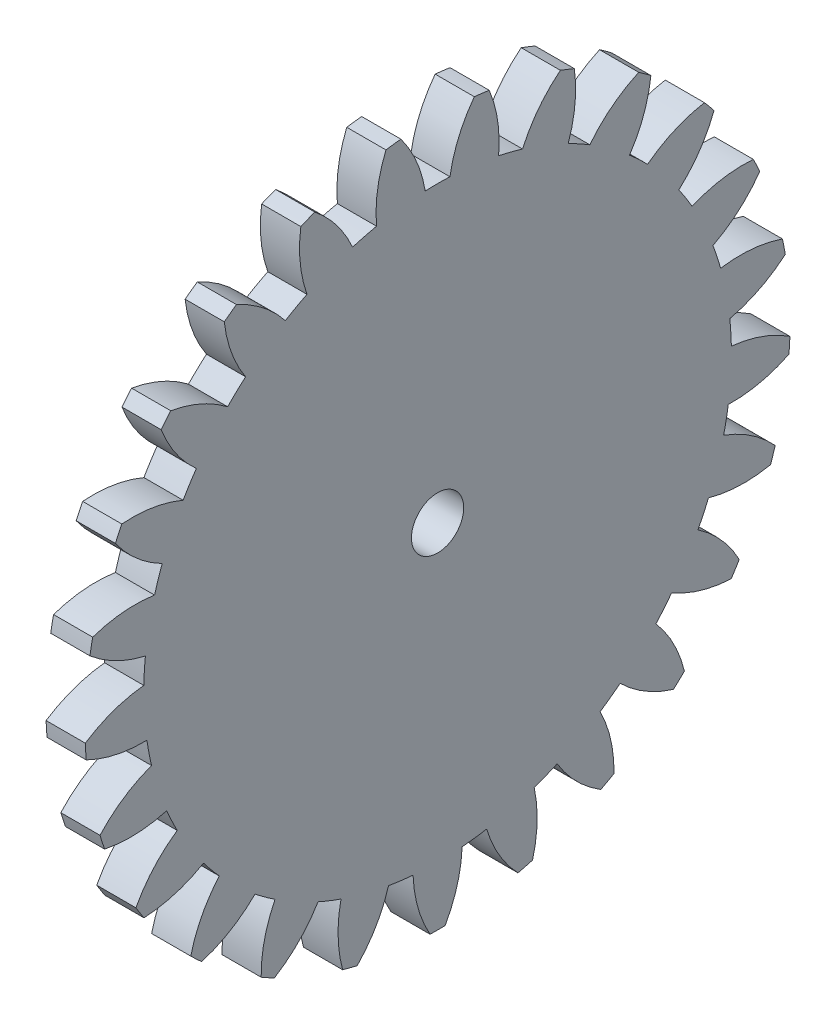
SolidWorks part; units mm, degrees
ref_plane "Plane1" through (0, 0, 0) normal (0, 0, 1) x (1, 0, 0)
ref_plane "Plane2" through (0, 0, 0) normal (0, 1, 0) x (1, 0, 0)
ref_plane "Plane3" through (0, 0, 0) normal (1, 0, 0) x (0, 0, -1)
other "Configuration Table"
sketch "HoldingSke" plane through (0, 0, 0) normal (0, 1, 0) x (1, 0, 0)
  line L0 (0, 0) -> (0.4532, -0.2113)
  line L1 (-15, 0) -> (100, 0) construction
  line L2 (0, 0) -> (-2.1039, 2.3779)
  line L3 (0, 0) -> (-11.863, 4.5341)
  line L4 (0, 0) -> (7.8269, 3.6497)
  line L5 (0, 0) -> (-46.8476, -17.4728)
  line L6 (0, 0) -> (-2.4869, -1.6779)
  line L7 (-2.1039, 2.3779) -> (8.6586, 51.2059)
  line L8 (-76.2, 54.61) -> (-75.5, 54.61)
  line L9 (-71.009, 38.7566) -> (-53.1078, 45.2721)
  line L10 (-76.2, 71.12) -> (104.1128, 71.12)
  line L11 (0, 0) -> (-3, 0)
  line L12 (-76.2, 101.6) -> (-76.133, 101.6)
  line L13 (24.9733, 27.94) -> (52.9518, 28.4284)
  line L14 (24.9733, 27.94) -> (24.9743, 27.94)
  line L15 (24.9733, 27.94) -> (100.4006, 29.5858)
  line L16 (-63.627, -2) -> (-12.827, -2)
  circle A0 centre (0, 0) radius 2
  circle A1 centre (0, 0) radius 22.499
  circle A2 centre (0, 0) radius 37.5
  circle A3 centre (0, 0) radius 2
  dimension "Hub_dia" = 75
  dimension "Bore" = 4
  dimension "MBD" = 4
  dimension "Num_teeth" = 25
  dimension "Overall_len" = 50
  dimension "Show_teeth" = 25
  dimension "Thickness" = 3
  dimension "OAL" = 50.0001
  dimension "T_dim" = 0.7
  dimension "Ap" = 20
  dimension "H" = 19.05
  dimension "Pitch_radius" = 180.3128
  dimension "Width" = 3
  dimension "Addendum_fac" = 1
  dimension "Dedendum_fac" = 1.25
  dimension "Clearance_fac" = 0.25
  dimension "Dedendum_add" = 0.001
sketch "BasProSke" plane through (0, 0, 0) normal (0, 1, 0) x (1, 0, 0)
  line L0 (-10, 0) -> (60, 0) construction
  line L1 (0, 0) -> (0, 27)
  line L2 (0, 0) -> (3, 0)
  line L3 (3, 0) -> (3, 27)
  line L4 (3, 27) -> (0, 27)
  dimension "Thickness" = 3
revolve "Base-Revolve" add sketch "BasProSke" angle 360 about L0
sketch "TooCutSke" plane through (0, 0, 0) normal (1, 0, 0) x (0, 0, -1)
  line L1 (0, 0) -> (0, 107) construction
  line L2 (0, 0) -> (-1.687, 24.943) construction
  line L3 (0, 0) -> (-6.2561, 49.5219) construction
  line L4 (-1.687, 24.943) -> (-3.128, 24.761) construction
  arc A0 (0.9462, 22.4791) -> (-0.9462, 22.4791) centre (0, 0) ccw
  arc A1 (2.8295, 26.8769) -> (-2.8295, 26.8769) centre (0, 0) ccw
  circle A2 centre (0, 0) radius 25 construction
  circle A3 centre (0, 0) radius 23.4923 construction
  arc A4 (-0.9462, 22.4791) -> (-2.8295, 26.8769) centre (-10.8135, 20.8556) ccw
  arc A5 (2.8295, 26.8769) -> (0.9462, 22.4791) centre (10.8135, 20.8556) ccw
  dimension "Half_ang" = 7.2
extrude "ToothCut" cut sketch "TooCutSke" along normal through all
fillet "Breaks" [suppressed] radius 0.04
fillet "RootFillets" [suppressed] radius 0.501
pattern_circular "TeethCuts" count 25 every 14.4 about axis through (-10, 0, 0) along (1, 0, 0) of "ToothCut", "RootFillets", "Breaks"
sketch "HubNeaOneSke" plane through (0, 0, 0) normal (-1, 0, 0) x (0, 0, 1)
  circle A0 centre (0, 0) radius 22.499
extrude "HubNearOne" [suppressed] add sketch "HubNeaOneSke" along normal blind 47.0001
sketch "HubNeaBotSke" plane through (0, 0, 0) normal (-1, 0, 0) x (0, 0, 1)
  circle A0 centre (0, 0) radius 22.499
extrude "HubNearBoth" [suppressed] add sketch "HubNeaBotSke" along normal blind 23.5
ref_plane "FarPln" through (3, 0, 0) normal (1, 0, 0) x (0, 0, -1)
sketch "HubFarSke" plane through (3, 0, 0) normal (1, 0, 0) x (0, 0, -1)
  circle A0 centre (0, 0) radius 22.499
extrude "HubFar" [suppressed] add sketch "HubFarSke" along normal blind 23.5
sketch "BorSke" plane through (0, 0, 0) normal (1, 0, 0) x (0, 0, -1)
  circle A0 centre (0, 0) radius 2
  dimension "Diameter" = 4
extrude "Bore" cut sketch "BorSke" along normal mid plane 100.0001
sketch "KeySke" plane through (0, 0, 0) normal (1, 0, 0) x (0, 0, -1)
  line L0 (-0.8, 0) -> (-0.8, 2.7)
  line L1 (-0.8, 2.7) -> (0.8, 2.7)
  line L2 (0.8, 2.7) -> (0.8, 0)
  line L3 (0, 0) -> (0, 34) construction
  line L4 (-0.8, 0) -> (0.8, 0)
  dimension "Offset" = 2.7
  dimension "Width" = 1.6
extrude "Keyway" [suppressed] cut sketch "KeySke" along normal mid plane 100.0001
pattern_circular "Keyway2" [suppressed] count 2 every 90 about axis through (-10, 0, 0) along (1, 0, 0)
equation "' \"Module@HoldingSke\" = 6.35"
equation "' \"Num_teeth@HoldingSke\" = 12"
equation "' \"Ap@HoldingSke\" =  20"
equation "' \"Ap@HoldingSke\" = 20"
equation "' \"Width@HoldingSke\" = 0.5 * 25.4"
equation "' \"Hub_dia@HoldingSke\"= 1 * 25.4"
equation "' \"Hub_dia@HoldingSke\" = 1 * 25.4"
equation "' \"Overall_len@HoldingSke\" = 1.0 * 25.4"
equation "' \"Bore@HoldingSke\" = 0.75 * 25.4"
equation "' \"T_dim@HoldingSke\" = 0.1 * 25.4"
equation "' \"Width@KeySke\" = 0.25 * 25.4"
equation "' \"Show_teeth@HoldingSke\" = 13"
equation "' \"Backlash@HoldingSke\" = 0.009 * 25.4"
equation "' \"Addendum_fac@HoldingSke\" = 1.0"
equation "' \"Dedendum_fac@HoldingSke\" = 1.25"
equation "' \"Dedendum_add@HoldingSke\" = 0.00005 * 25.4"
equation "' \"Clearance_fac@HoldingSke\" = 0.25"
equation "\"Pitch@HoldingSke\" = 1 / \"Module@HoldingSke\""
equation "\"Overcut_dia@TooCutSke\" = (\"Num_teeth@HoldingSke\" + 2 * \"Addendum_fac@HoldingSke\") / \"Pitch@HoldingSke\" + 0.002 * 25.4"
equation "\"Pitch_dia@TooCutSke\" = \"Num_teeth@HoldingSke\" / \"Pitch@HoldingSke\""
equation "\"Base_dia@TooCutSke\" = \"Num_teeth@HoldingSke\" / \"Pitch@HoldingSke\" * cos((\"Ap@HoldingSke\"  * 3.14159265 / 180))"
equation "\"Root_dia@TooCutSke\" = (\"Num_teeth@HoldingSke\" + 2) / \"Pitch@HoldingSke\" - 2 * (\"Addendum_fac@HoldingSke\" + \"Dedendum_fac@HoldingSke\") / \"Pitch@HoldingSke\" - \"Dedendum_add@HoldingSke\" * 2"
equation "\"Half_ang@TooCutSke\" = 180 / \"Num_teeth@HoldingSke\""
equation "\"Half_CT@TooCutSke\" = \"Num_teeth@HoldingSke\" / \"Pitch@HoldingSke\" * sin((3.14159265 / 2 / \"Num_teeth@HoldingSke\")) / 2 - 7 * \"Backlash@HoldingSke\" / 4"
equation "\"Flank_rad@TooCutSke\" = \"Num_teeth@HoldingSke\" / \"Pitch@HoldingSke\" / 5"
equation "\"Radius@RootFillets\" = \"Clearance_fac@HoldingSke\" / \"Pitch@HoldingSke\" + \"Dedendum_add@HoldingSke\""
equation "\"Break_rad@Breaks\" = 0.02 / \"Pitch@HoldingSke\""
equation "\"Thickness@HoldingSke\" = \"Width@HoldingSke\""
equation "\"OAL@HoldingSke\" = \"Thickness@HoldingSke\""
equation "\"MHD@HoldingSke\" = (\"Num_teeth@HoldingSke\" + 2) / \"Pitch@HoldingSke\" - 2 * (\"Addendum_fac@HoldingSke\" + \"Dedendum_fac@HoldingSke\")  / \"Pitch@HoldingSke\" - \"Dedendum_add@HoldingSke\" * 2"
equation "\"MBD@HoldingSke\" = (\"Num_teeth@HoldingSke\" + 2) / \"Pitch@HoldingSke\" - 2 * (\"Addendum_fac@HoldingSke\" + \"Dedendum_fac@HoldingSke\")  / \"Pitch@HoldingSke\" - \"Dedendum_add@HoldingSke\" * 2 - 0.002 * 25.4"
equation "\"MHD@HoldingSke\" = ((sgn( \"MHD@HoldingSke\" - \"Hub_dia@HoldingSke\" )-1)*( \"MHD@HoldingSke\" - \"Hub_dia@HoldingSke\" ))/-2+ \"Hub_dia@HoldingSke\""
equation "\"MBD@HoldingSke\" = ((sgn( \"MBD@HoldingSke\" - \"Bore@HoldingSke\" )-1)*( \"MBD@HoldingSke\" - \"Bore@HoldingSke\" ))/-2+ \"Bore@HoldingSke\""
equation "\"OAL@HoldingSke\" = ((sgn( \"OAL@HoldingSke\" - \"Overall_len@HoldingSke\" )+1)*( \"OAL@HoldingSke\" - \"Overall_len@HoldingSke\" ))/2 + \"Overall_len@HoldingSke\" + 0.000002 * 25.4"
equation "\"Num_teeth@TeethCuts\" = int( \"Show_teeth@HoldingSke\" ) + 1"
equation "\"Num_teeth@TeethCuts\" = ((sgn( \"Num_teeth@TeethCuts\" - \"Num_teeth@HoldingSke\" )-1)*( \"Num_teeth@TeethCuts\" - \"Num_teeth@HoldingSke\" ))/-2+ \"Num_teeth@HoldingSke\""
equation "\"Num_teeth@TeethCuts\" = ((sgn( \"Num_teeth@TeethCuts\" - 2.0)+1)*( \"Num_teeth@TeethCuts\" - 2.0))/2 +2.0"
equation "\"Angle@TeethCuts\" = 360.0 / \"Num_teeth@HoldingSke\""
equation "\"Diameter@BasProSke\" = (\"Num_teeth@HoldingSke\" + 2 * \"Addendum_fac@HoldingSke\") / \"Pitch@HoldingSke\""
equation "\"Thickness@BasProSke\"  = \"Thickness@HoldingSke\""
equation "' \"Fillet_rad@BasProSke\" =  \"Thickness@HoldingSke\" * 0.05"
equation "' \"Fillet_rad@BasProSke\" = \"Thickness@HoldingSke\" * 0.05"
equation "\"MHD@HoldingSke\" = ((sgn( \"MHD@HoldingSke\" - \"Root_dia@TooCutSke\" )-1)*( \"MHD@HoldingSke\" - \"Root_dia@TooCutSke\" ))/-2+ \"Root_dia@TooCutSke\""
equation "\"Diameter@HubNeaOneSke\" = \"MHD@HoldingSke\""
equation "\"Length@HubNearOne\" = \"OAL@HoldingSke\" - \"Thickness@BasProSke\""
equation "\"Diameter@HubNeaBotSke\" = \"MHD@HoldingSke\""
equation "\"Length@HubNearBoth\" = ( \"OAL@HoldingSke\" - \"Thickness@BasProSke\" ) / 2.0"
equation "\"Thickness@FarPln\" = \"Thickness@BasProSke\""
equation "\"Diameter@HubFarSke\" = \"MHD@HoldingSke\""
equation "\"Length@HubFar\" = ( \"OAL@HoldingSke\" - \"Thickness@BasProSke\" ) / 2.0"
equation "\"Diameter@BorSke\" = \"MBD@HoldingSke\""
equation "\"D1@Bore\" = \"OAL@HoldingSke\" * 2.0"
equation "\"D1@Keyway\" = \"OAL@HoldingSke\" * 2.0"
equation "\"Offset@KeySke\" = \"T_dim@HoldingSke\" + \"MBD@HoldingSke\" / 2.0"
